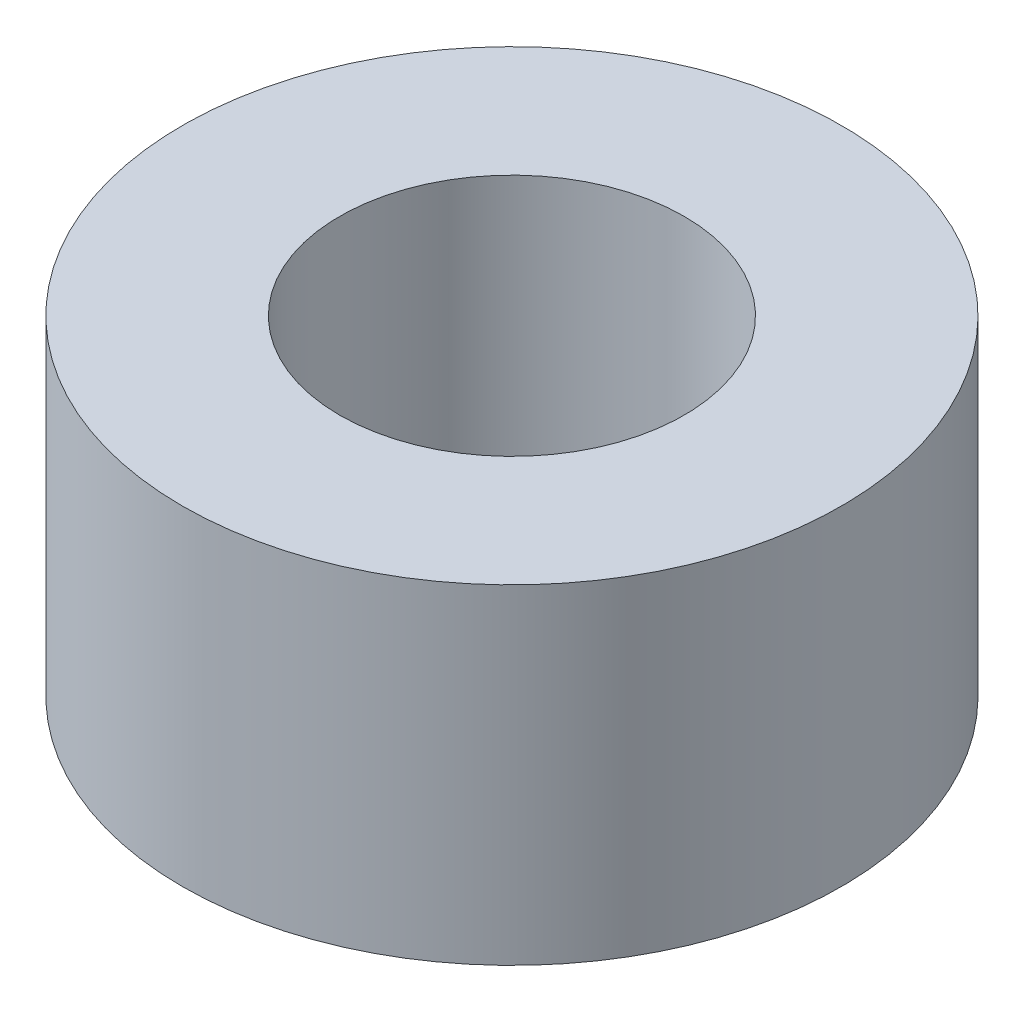
SolidWorks part; units mm, degrees
material "6061 Alloy"
ref_plane "Front Plane" through (0, 0, 0) normal (0, 0, 1) x (1, 0, 0)
ref_plane "Top Plane" through (0, 0, 0) normal (0, 1, 0) x (1, 0, 0)
ref_plane "Right Plane" through (0, 0, 0) normal (1, 0, 0) x (0, 0, -1)
sketch "Sketch1" plane through (0, 0, 0) normal (0, 1, 0) x (1, 0, 0)
  circle A0 centre (0, 0) radius 2.4892
  circle A1 centre (0, 0) radius 4.7625
  dimension "D1" = 4.9784
  dimension "D2" = 9.525
extrude "Boss-Extrude1" add sketch "Sketch1" along normal blind 4.7625
